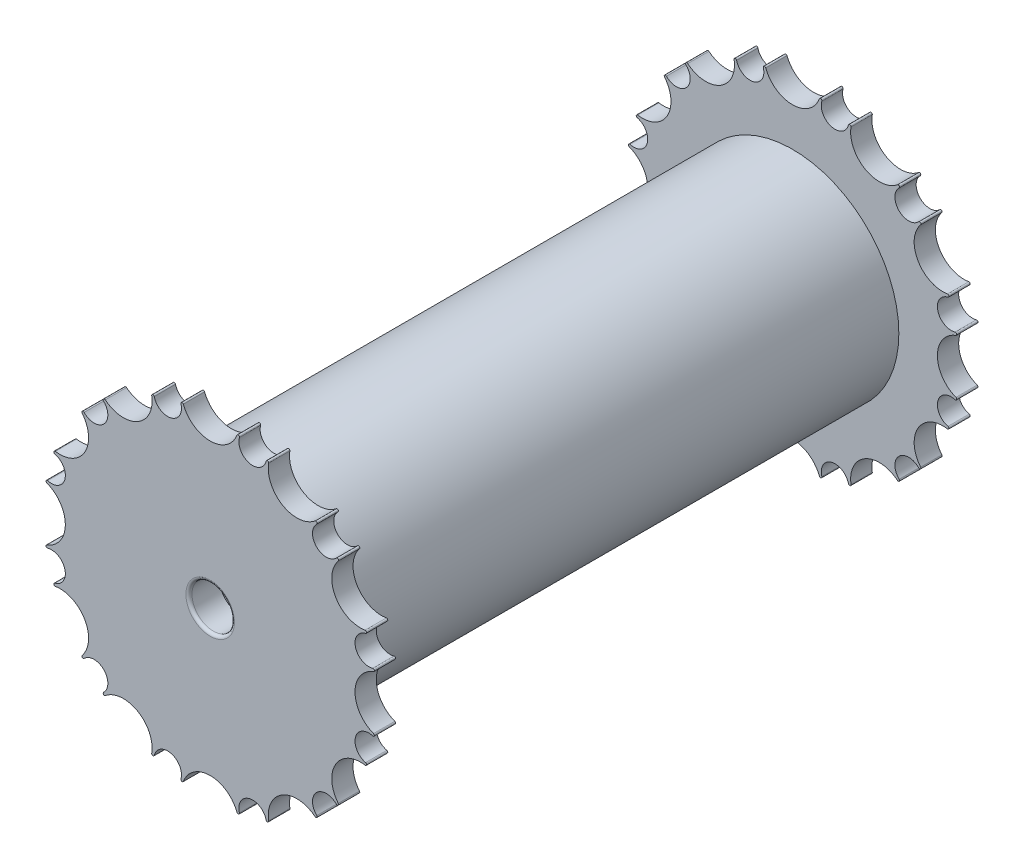
SolidWorks part; units mm, degrees
ref_plane "Front Plane" through (0, 0, 0) normal (0, 0, 1) x (1, 0, 0)
ref_plane "Top Plane" through (0, 0, 0) normal (0, 1, 0) x (1, 0, 0)
ref_plane "Right Plane" through (0, 0, 0) normal (1, 0, 0) x (0, 0, -1)
sketch "Sketch1" plane through (0, 0, 0) normal (0, 0, 1) x (1, 0, 0)
  line L1 (5, -18.6603) -> (13.6603, -13.6603)
  line L2 (13.6603, -13.6603) -> (18.6603, -5)
  line L3 (18.6603, -5) -> (18.6603, 5)
  line L4 (18.6603, 5) -> (13.6603, 13.6603)
  line L5 (13.6603, 13.6603) -> (5, 18.6603)
  line L6 (5, 18.6603) -> (-5, 18.6603)
  line L7 (-5, 18.6603) -> (-13.6603, 13.6603)
  line L8 (-13.6603, 13.6603) -> (-18.6603, 5)
  line L9 (-18.6603, 5) -> (-18.6603, -5)
  line L10 (-18.6603, -5) -> (-13.6603, -13.6603)
  line L11 (-13.6603, -13.6603) -> (-5, -18.6603)
  line L12 (-5, -18.6603) -> (5, -18.6603)
  circle A0 centre (0, 0) radius 18.6603 construction
  circle A1 centre (-5, 18.6603) radius 1.5 construction
  circle A2 centre (5, 18.6603) radius 1.5 construction
  circle A3 centre (-5, 18.6603) radius 1.625
  circle A4 centre (5, 18.6603) radius 1.625
  circle A5 centre (0, 20.4103) radius 3.375 construction
  arc A6 (-3.4408, 19.1179) -> (-3.1557, 19.2136) centre (-3.2964, 19.1603) cw
  arc A7 (3.1557, 19.2136) -> (3.4408, 19.1179) centre (3.2964, 19.1603) cw
  point P1 (0, 18.6603)
  dimension "D2" = 3
  dimension "D5" = 6.75
  dimension "D1" = 10
  dimension "D6" = 1.75
  dimension "D7" = 0.5
  dimension "D3" = 0.125
  dimension "D4" = 0.125
sketch "Sketch10" plane through (0, 0, 0) normal (0, 0, 1) x (1, 0, 0)
  line L2 (-5, -18.6603) -> (5, -18.6603) construction
  line L14 (-3.375, -18.6603) -> (-2.8858, -18.6603)
  circle A0 centre (5, 18.6603) radius 1.625 construction
  arc A1 (3.4408, 19.1179) -> (3.1557, 19.2136) centre (3.2964, 19.1603) ccw construction
  circle A2 centre (0, 20.4103) radius 3.375 construction
  arc A3 (-3.1557, 19.2136) -> (-3.4408, 19.1179) centre (-3.2964, 19.1603) ccw construction
  circle A4 centre (-5, 18.6603) radius 1.625 construction
  arc A5 (3.4408, 19.1179) -> (6.5791, 18.277) centre (5, 18.6603) ccw
  arc A6 (3.4408, 19.1179) -> (3.1557, 19.2136) centre (3.2964, 19.1603) ccw
  arc A7 (-3.1557, 19.2136) -> (3.1557, 19.2136) centre (0, 20.4103) ccw
  arc A8 (-3.1557, 19.2136) -> (-3.4408, 19.1179) centre (-3.2964, 19.1603) ccw
  arc A9 (-6.4073, 17.8478) -> (-3.4408, 19.1179) centre (-5, 18.6603) ccw
  circle A12 centre (0, 0) radius 12.5
  arc A14 (3.375, 18.6603) -> (6.5791, 18.277) centre (5, 18.6603) ccw
  arc A15 (6.8739, 18.2173) -> (6.5791, 18.277) centre (6.7254, 18.2415) ccw
  arc A16 (6.8739, 18.2173) -> (12.3397, 15.0616) centre (10.2051, 17.6758) ccw
  arc A17 (12.5387, 14.8362) -> (12.3397, 15.0616) centre (12.4349, 14.9451) ccw
  arc A18 (12.5387, 14.8362) -> (14.8362, 12.5387) centre (13.6603, 13.6603) ccw
  arc A19 (12.253, 14.4728) -> (14.8362, 12.5387) centre (13.6603, 13.6603) ccw
  arc A20 (15.0616, 12.3397) -> (14.8362, 12.5387) centre (14.9451, 12.4349) ccw
  arc A21 (15.0616, 12.3397) -> (18.2173, 6.8739) centre (17.6758, 10.2051) ccw
  arc A22 (18.277, 6.5791) -> (18.2173, 6.8739) centre (18.2415, 6.7254) ccw
  arc A23 (18.277, 6.5791) -> (19.1179, 3.4408) centre (18.6603, 5) ccw
  arc A24 (17.8478, 6.4073) -> (19.1179, 3.4408) centre (18.6603, 5) ccw
  arc A25 (19.2136, 3.1557) -> (19.1179, 3.4408) centre (19.1603, 3.2964) ccw
  arc A26 (19.2136, 3.1557) -> (19.2136, -3.1557) centre (20.4103, 0) ccw
  arc A27 (19.1179, -3.4408) -> (19.2136, -3.1557) centre (19.1603, -3.2964) ccw
  arc A28 (19.1179, -3.4408) -> (18.277, -6.5791) centre (18.6603, -5) ccw
  arc A29 (18.6603, -3.375) -> (18.277, -6.5791) centre (18.6603, -5) ccw
  arc A30 (18.2173, -6.8739) -> (18.277, -6.5791) centre (18.2415, -6.7254) ccw
  arc A31 (18.2173, -6.8739) -> (15.0616, -12.3397) centre (17.6758, -10.2051) ccw
  arc A32 (14.8362, -12.5387) -> (15.0616, -12.3397) centre (14.9451, -12.4349) ccw
  arc A33 (14.8362, -12.5387) -> (12.5387, -14.8362) centre (13.6603, -13.6603) ccw
  arc A34 (14.4728, -12.253) -> (12.5387, -14.8362) centre (13.6603, -13.6603) ccw
  arc A35 (12.3397, -15.0616) -> (12.5387, -14.8362) centre (12.4349, -14.9451) ccw
  arc A36 (12.3397, -15.0616) -> (6.8739, -18.2173) centre (10.2051, -17.6758) ccw
  arc A37 (6.5791, -18.277) -> (6.8739, -18.2173) centre (6.7254, -18.2415) ccw
  arc A38 (6.5791, -18.277) -> (3.4408, -19.1179) centre (5, -18.6603) ccw
  arc A39 (6.4073, -17.8478) -> (3.4408, -19.1179) centre (5, -18.6603) ccw
  arc A40 (3.1557, -19.2136) -> (3.4408, -19.1179) centre (3.2964, -19.1603) ccw
  arc A41 (3.1557, -19.2136) -> (-3.1557, -19.2136) centre (0, -20.4103) ccw
  arc A42 (-3.4408, -19.1179) -> (-3.1557, -19.2136) centre (-3.2964, -19.1603) ccw
  arc A43 (-3.4408, -19.1179) -> (-6.5791, -18.277) centre (-5, -18.6603) ccw
  arc A44 (-3.375, -18.6603) -> (-6.5791, -18.277) centre (-5, -18.6603) ccw
  arc A45 (-6.8739, -18.2173) -> (-6.5791, -18.277) centre (-6.7254, -18.2415) ccw
  arc A46 (-6.8739, -18.2173) -> (-12.3397, -15.0616) centre (-10.2051, -17.6758) ccw
  arc A47 (-12.5387, -14.8362) -> (-12.3397, -15.0616) centre (-12.4349, -14.9451) ccw
  arc A48 (-12.5387, -14.8362) -> (-14.8362, -12.5387) centre (-13.6603, -13.6603) ccw
  arc A49 (-12.253, -14.4728) -> (-14.8362, -12.5387) centre (-13.6603, -13.6603) ccw
  arc A50 (-15.0616, -12.3397) -> (-14.8362, -12.5387) centre (-14.9451, -12.4349) ccw
  arc A51 (-15.0616, -12.3397) -> (-18.2173, -6.8739) centre (-17.6758, -10.2051) ccw
  arc A52 (-18.277, -6.5791) -> (-18.2173, -6.8739) centre (-18.2415, -6.7254) ccw
  arc A53 (-18.277, -6.5791) -> (-19.1179, -3.4408) centre (-18.6603, -5) ccw
  arc A54 (-17.8478, -6.4073) -> (-19.1179, -3.4408) centre (-18.6603, -5) ccw
  arc A55 (-19.2136, -3.1557) -> (-19.1179, -3.4408) centre (-19.1603, -3.2964) ccw
  arc A56 (-19.2136, -3.1557) -> (-19.2136, 3.1557) centre (-20.4103, 0) ccw
  arc A57 (-19.1179, 3.4408) -> (-19.2136, 3.1557) centre (-19.1603, 3.2964) ccw
  arc A58 (-19.1179, 3.4408) -> (-18.277, 6.5791) centre (-18.6603, 5) ccw
  arc A59 (-18.6603, 3.375) -> (-18.277, 6.5791) centre (-18.6603, 5) ccw
  arc A60 (-18.2173, 6.8739) -> (-18.277, 6.5791) centre (-18.2415, 6.7254) ccw
  arc A61 (-18.2173, 6.8739) -> (-15.0616, 12.3397) centre (-17.6758, 10.2051) ccw
  arc A62 (-14.8362, 12.5387) -> (-15.0616, 12.3397) centre (-14.9451, 12.4349) ccw
  arc A63 (-14.8362, 12.5387) -> (-12.5387, 14.8362) centre (-13.6603, 13.6603) ccw
  arc A64 (-14.4728, 12.253) -> (-12.5387, 14.8362) centre (-13.6603, 13.6603) ccw
  arc A65 (-12.3397, 15.0616) -> (-12.5387, 14.8362) centre (-12.4349, 14.9451) ccw
  arc A66 (-12.3397, 15.0616) -> (-6.8739, 18.2173) centre (-10.2051, 17.6758) ccw
  arc A67 (-6.5791, 18.277) -> (-6.8739, 18.2173) centre (-6.7254, 18.2415) ccw
  arc A68 (-6.5791, 18.277) -> (-3.4408, 19.1179) centre (-5, 18.6603) ccw
  point P162 (0, 0)
  dimension "D2" = 25
  dimension "D1" = 12
sketch "Sketch2" plane through (0, 0, 0) normal (0, 0, 1) x (1, 0, 0)
  line L0 (-10, 37.3205) -> (0, 0) construction
  line L1 (0, 0) -> (10, 37.3205) construction
  arc A5 (6.8815, 38.2358) -> (6.3115, 38.4272) centre (6.5928, 38.3205) ccw
  arc A6 (6.8815, 38.2358) -> (9.1588, 34.1812) centre (10, 37.3205) ccw
  arc A7 (-6.3115, 38.4272) -> (6.3115, 38.4272) centre (0, 40.8205) ccw
  arc A8 (-6.3115, 38.4272) -> (-6.8815, 38.2358) centre (-6.5928, 38.3205) ccw
  arc A9 (-9.1588, 34.1812) -> (-6.8815, 38.2358) centre (-10, 37.3205) ccw
  arc A10 (9.1588, 34.1812) -> (13.1583, 36.5539) centre (10, 37.3205) ccw
  arc A11 (13.7477, 36.4347) -> (13.1583, 36.5539) centre (13.4507, 36.4829) ccw
  arc A12 (13.7477, 36.4347) -> (24.6795, 30.1232) centre (20.4103, 35.3516) ccw
  arc A13 (25.0775, 29.6724) -> (24.6795, 30.1232) centre (24.8698, 29.8901) ccw
  arc A14 (25.0775, 29.6724) -> (25.0224, 25.0224) centre (27.3205, 27.3205) ccw
  arc A15 (25.0224, 25.0224) -> (29.6724, 25.0775) centre (27.3205, 27.3205) ccw
  arc A16 (30.1232, 24.6795) -> (29.6724, 25.0775) centre (29.8901, 24.8698) ccw
  arc A17 (30.1232, 24.6795) -> (36.4347, 13.7477) centre (35.3516, 20.4103) ccw
  arc A18 (36.5539, 13.1583) -> (36.4347, 13.7477) centre (36.4829, 13.4507) ccw
  arc A19 (36.5539, 13.1583) -> (34.1812, 9.1588) centre (37.3205, 10) ccw
  arc A20 (34.1812, 9.1588) -> (38.2358, 6.8815) centre (37.3205, 10) ccw
  arc A21 (38.4272, 6.3115) -> (38.2358, 6.8815) centre (38.3205, 6.5928) ccw
  arc A22 (38.4272, 6.3115) -> (38.4272, -6.3115) centre (40.8205, 0) ccw
  arc A23 (38.2358, -6.8815) -> (38.4272, -6.3115) centre (38.3205, -6.5928) ccw
  arc A24 (38.2358, -6.8815) -> (34.1812, -9.1588) centre (37.3205, -10) ccw
  arc A25 (34.1812, -9.1588) -> (36.5539, -13.1583) centre (37.3205, -10) ccw
  arc A26 (36.4347, -13.7477) -> (36.5539, -13.1583) centre (36.4829, -13.4507) ccw
  arc A27 (36.4347, -13.7477) -> (30.1232, -24.6795) centre (35.3516, -20.4103) ccw
  arc A28 (29.6724, -25.0775) -> (30.1232, -24.6795) centre (29.8901, -24.8698) ccw
  arc A29 (29.6724, -25.0775) -> (25.0224, -25.0224) centre (27.3205, -27.3205) ccw
  arc A30 (25.0224, -25.0224) -> (25.0775, -29.6724) centre (27.3205, -27.3205) ccw
  arc A31 (24.6795, -30.1232) -> (25.0775, -29.6724) centre (24.8698, -29.8901) ccw
  arc A32 (24.6795, -30.1232) -> (13.7477, -36.4347) centre (20.4103, -35.3516) ccw
  arc A33 (13.1583, -36.5539) -> (13.7477, -36.4347) centre (13.4507, -36.4829) ccw
  arc A34 (13.1583, -36.5539) -> (9.1588, -34.1812) centre (10, -37.3205) ccw
  arc A35 (9.1588, -34.1812) -> (6.8815, -38.2358) centre (10, -37.3205) ccw
  arc A36 (6.3115, -38.4272) -> (6.8815, -38.2358) centre (6.5928, -38.3205) ccw
  arc A37 (6.3115, -38.4272) -> (-6.3115, -38.4272) centre (0, -40.8205) ccw
  arc A38 (-6.8815, -38.2358) -> (-6.3115, -38.4272) centre (-6.5928, -38.3205) ccw
  arc A39 (-6.8815, -38.2358) -> (-9.1588, -34.1812) centre (-10, -37.3205) ccw
  arc A40 (-9.1588, -34.1812) -> (-13.1583, -36.5539) centre (-10, -37.3205) ccw
  arc A41 (-13.7477, -36.4347) -> (-13.1583, -36.5539) centre (-13.4507, -36.4829) ccw
  arc A42 (-13.7477, -36.4347) -> (-24.6795, -30.1232) centre (-20.4103, -35.3516) ccw
  arc A43 (-25.0775, -29.6724) -> (-24.6795, -30.1232) centre (-24.8698, -29.8901) ccw
  arc A44 (-25.0775, -29.6724) -> (-25.0224, -25.0224) centre (-27.3205, -27.3205) ccw
  arc A45 (-25.0224, -25.0224) -> (-29.6724, -25.0775) centre (-27.3205, -27.3205) ccw
  arc A46 (-30.1232, -24.6795) -> (-29.6724, -25.0775) centre (-29.8901, -24.8698) ccw
  arc A47 (-30.1232, -24.6795) -> (-36.4347, -13.7477) centre (-35.3516, -20.4103) ccw
  arc A48 (-36.5539, -13.1583) -> (-36.4347, -13.7477) centre (-36.4829, -13.4507) ccw
  arc A49 (-36.5539, -13.1583) -> (-34.1812, -9.1588) centre (-37.3205, -10) ccw
  arc A50 (-34.1812, -9.1588) -> (-38.2358, -6.8815) centre (-37.3205, -10) ccw
  arc A51 (-38.4272, -6.3115) -> (-38.2358, -6.8815) centre (-38.3205, -6.5928) ccw
  arc A52 (-38.4272, -6.3115) -> (-38.4272, 6.3115) centre (-40.8205, 0) ccw
  arc A53 (-38.2358, 6.8815) -> (-38.4272, 6.3115) centre (-38.3205, 6.5928) ccw
  arc A54 (-38.2358, 6.8815) -> (-34.1812, 9.1588) centre (-37.3205, 10) ccw
  arc A55 (-34.1812, 9.1588) -> (-36.5539, 13.1583) centre (-37.3205, 10) ccw
  arc A56 (-36.4347, 13.7477) -> (-36.5539, 13.1583) centre (-36.4829, 13.4507) ccw
  arc A57 (-36.4347, 13.7477) -> (-30.1232, 24.6795) centre (-35.3516, 20.4103) ccw
  arc A58 (-29.6724, 25.0775) -> (-30.1232, 24.6795) centre (-29.8901, 24.8698) ccw
  arc A59 (-29.6724, 25.0775) -> (-25.0224, 25.0224) centre (-27.3205, 27.3205) ccw
  arc A60 (-25.0224, 25.0224) -> (-25.0775, 29.6724) centre (-27.3205, 27.3205) ccw
  arc A61 (-24.6795, 30.1232) -> (-25.0775, 29.6724) centre (-24.8698, 29.8901) ccw
  arc A62 (-24.6795, 30.1232) -> (-13.7477, 36.4347) centre (-20.4103, 35.3516) ccw
  arc A63 (-13.1583, 36.5539) -> (-13.7477, 36.4347) centre (-13.4507, 36.4829) ccw
  arc A64 (-13.1583, 36.5539) -> (-9.1588, 34.1812) centre (-10, 37.3205) ccw
  circle A65 centre (0, 0) radius 30
  point P139 (0, 0)
  dimension "D2" = 60
  dimension "D3" = 6.75
  dimension "D1" = 12
sketch "Sketch4" plane through (0, 0, 0) normal (0, 0, 1) x (1, 0, 0)
  arc A62 (-24.6795, 30.1232) -> (-25.0775, 29.6724) centre (-24.8698, 29.8901) ccw
  arc A63 (-24.6795, 30.1232) -> (-13.7477, 36.4347) centre (-20.4103, 35.3516) ccw
  arc A64 (-13.1583, 36.5539) -> (-13.7477, 36.4347) centre (-13.4507, 36.4829) ccw
  arc A65 (-13.1583, 36.5539) -> (-9.1588, 34.1812) centre (-10, 37.3205) ccw
  arc A66 (-9.1588, 34.1812) -> (-6.8815, 38.2358) centre (-10, 37.3205) ccw
  arc A67 (-6.3115, 38.4272) -> (-6.8815, 38.2358) centre (-6.5928, 38.3205) ccw
  arc A68 (-6.3115, 38.4272) -> (6.3115, 38.4272) centre (0, 40.8205) ccw
  arc A69 (6.8815, 38.2358) -> (6.3115, 38.4272) centre (6.5928, 38.3205) ccw
  arc A70 (6.8815, 38.2358) -> (9.1588, 34.1812) centre (10, 37.3205) ccw
  arc A71 (9.1588, 34.1812) -> (13.1583, 36.5539) centre (10, 37.3205) ccw
  arc A72 (13.7477, 36.4347) -> (13.1583, 36.5539) centre (13.4507, 36.4829) ccw
  arc A73 (13.7477, 36.4347) -> (24.6795, 30.1232) centre (20.4103, 35.3516) ccw
  arc A74 (25.0775, 29.6724) -> (24.6795, 30.1232) centre (24.8698, 29.8901) ccw
  arc A75 (25.0775, 29.6724) -> (25.0224, 25.0224) centre (27.3205, 27.3205) ccw
  arc A76 (25.0224, 25.0224) -> (29.6724, 25.0775) centre (27.3205, 27.3205) ccw
  arc A77 (30.1232, 24.6795) -> (29.6724, 25.0775) centre (29.8901, 24.8698) ccw
  arc A78 (30.1232, 24.6795) -> (36.4347, 13.7477) centre (35.3516, 20.4103) ccw
  arc A79 (36.5539, 13.1583) -> (36.4347, 13.7477) centre (36.4829, 13.4507) ccw
  arc A80 (36.5539, 13.1583) -> (34.1812, 9.1588) centre (37.3205, 10) ccw
  arc A81 (34.1812, 9.1588) -> (38.2358, 6.8815) centre (37.3205, 10) ccw
  arc A82 (38.4272, 6.3115) -> (38.2358, 6.8815) centre (38.3205, 6.5928) ccw
  arc A83 (38.4272, 6.3115) -> (38.4272, -6.3115) centre (40.8205, 0) ccw
  arc A84 (38.2358, -6.8815) -> (38.4272, -6.3115) centre (38.3205, -6.5928) ccw
  arc A85 (38.2358, -6.8815) -> (34.1812, -9.1588) centre (37.3205, -10) ccw
  arc A86 (34.1812, -9.1588) -> (36.5539, -13.1583) centre (37.3205, -10) ccw
  arc A87 (36.4347, -13.7477) -> (36.5539, -13.1583) centre (36.4829, -13.4507) ccw
  arc A88 (36.4347, -13.7477) -> (30.1232, -24.6795) centre (35.3516, -20.4103) ccw
  arc A89 (29.6724, -25.0775) -> (30.1232, -24.6795) centre (29.8901, -24.8698) ccw
  arc A90 (29.6724, -25.0775) -> (25.0224, -25.0224) centre (27.3205, -27.3205) ccw
  arc A91 (25.0224, -25.0224) -> (25.0775, -29.6724) centre (27.3205, -27.3205) ccw
  arc A92 (24.6795, -30.1232) -> (25.0775, -29.6724) centre (24.8698, -29.8901) ccw
  arc A93 (24.6795, -30.1232) -> (13.7477, -36.4347) centre (20.4103, -35.3516) ccw
  arc A94 (13.1583, -36.5539) -> (13.7477, -36.4347) centre (13.4507, -36.4829) ccw
  arc A95 (13.1583, -36.5539) -> (9.1588, -34.1812) centre (10, -37.3205) ccw
  arc A96 (9.1588, -34.1812) -> (6.8815, -38.2358) centre (10, -37.3205) ccw
  arc A97 (6.3115, -38.4272) -> (6.8815, -38.2358) centre (6.5928, -38.3205) ccw
  arc A98 (6.3115, -38.4272) -> (-6.3115, -38.4272) centre (0, -40.8205) ccw
  arc A99 (-6.8815, -38.2358) -> (-6.3115, -38.4272) centre (-6.5928, -38.3205) ccw
  arc A100 (-6.8815, -38.2358) -> (-9.1588, -34.1812) centre (-10, -37.3205) ccw
  arc A101 (-9.1588, -34.1812) -> (-13.1583, -36.5539) centre (-10, -37.3205) ccw
  arc A102 (-13.7477, -36.4347) -> (-13.1583, -36.5539) centre (-13.4507, -36.4829) ccw
  arc A103 (-13.7477, -36.4347) -> (-24.6795, -30.1232) centre (-20.4103, -35.3516) ccw
  arc A104 (-25.0775, -29.6724) -> (-24.6795, -30.1232) centre (-24.8698, -29.8901) ccw
  arc A105 (-25.0775, -29.6724) -> (-25.0224, -25.0224) centre (-27.3205, -27.3205) ccw
  arc A106 (-25.0224, -25.0224) -> (-29.6724, -25.0775) centre (-27.3205, -27.3205) ccw
  arc A107 (-30.1232, -24.6795) -> (-29.6724, -25.0775) centre (-29.8901, -24.8698) ccw
  arc A108 (-30.1232, -24.6795) -> (-36.4347, -13.7477) centre (-35.3516, -20.4103) ccw
  arc A109 (-36.5539, -13.1583) -> (-36.4347, -13.7477) centre (-36.4829, -13.4507) ccw
  arc A110 (-36.5539, -13.1583) -> (-34.1812, -9.1588) centre (-37.3205, -10) ccw
  arc A111 (-34.1812, -9.1588) -> (-38.2358, -6.8815) centre (-37.3205, -10) ccw
  arc A112 (-38.4272, -6.3115) -> (-38.2358, -6.8815) centre (-38.3205, -6.5928) ccw
  arc A113 (-38.4272, -6.3115) -> (-38.4272, 6.3115) centre (-40.8205, 0) ccw
  arc A114 (-38.2358, 6.8815) -> (-38.4272, 6.3115) centre (-38.3205, 6.5928) ccw
  arc A115 (-38.2358, 6.8815) -> (-34.1812, 9.1588) centre (-37.3205, 10) ccw
  arc A116 (-34.1812, 9.1588) -> (-36.5539, 13.1583) centre (-37.3205, 10) ccw
  arc A117 (-36.4347, 13.7477) -> (-36.5539, 13.1583) centre (-36.4829, 13.4507) ccw
  arc A118 (-36.4347, 13.7477) -> (-30.1232, 24.6795) centre (-35.3516, 20.4103) ccw
  arc A119 (-29.6724, 25.0775) -> (-30.1232, 24.6795) centre (-29.8901, 24.8698) ccw
  arc A120 (-29.6724, 25.0775) -> (-25.0224, 25.0224) centre (-27.3205, 27.3205) ccw
  arc A121 (-25.0224, 25.0224) -> (-25.0775, 29.6724) centre (-27.3205, 27.3205) ccw
  arc A122 (-24.6795, 30.1232) -> (-25.0775, 29.6724) centre (-24.8698, 29.8901) ccw
  arc A123 (-24.6795, 30.1232) -> (-13.7477, 36.4347) centre (-20.4103, 35.3516) ccw
  arc A124 (-13.1583, 36.5539) -> (-13.7477, 36.4347) centre (-13.4507, 36.4829) ccw
  arc A125 (-13.1583, 36.5539) -> (-9.1588, 34.1812) centre (-10, 37.3205) ccw
  arc A126 (-9.1588, 34.1812) -> (-6.8815, 38.2358) centre (-10, 37.3205) ccw
  arc A127 (-6.3115, 38.4272) -> (-6.8815, 38.2358) centre (-6.5928, 38.3205) ccw
  arc A128 (-6.3115, 38.4272) -> (6.3115, 38.4272) centre (0, 40.8205) ccw
  arc A129 (6.8815, 38.2358) -> (6.3115, 38.4272) centre (6.5928, 38.3205) ccw
  arc A130 (6.8815, 38.2358) -> (9.1588, 34.1812) centre (10, 37.3205) ccw
  arc A131 (9.1588, 34.1812) -> (13.1583, 36.5539) centre (10, 37.3205) ccw
  arc A132 (13.7477, 36.4347) -> (13.1583, 36.5539) centre (13.4507, 36.4829) ccw
  arc A133 (13.7477, 36.4347) -> (24.6795, 30.1232) centre (20.4103, 35.3516) ccw
  arc A134 (25.0775, 29.6724) -> (24.6795, 30.1232) centre (24.8698, 29.8901) ccw
  arc A135 (25.0775, 29.6724) -> (25.0224, 25.0224) centre (27.3205, 27.3205) ccw
  arc A136 (25.0224, 25.0224) -> (29.6724, 25.0775) centre (27.3205, 27.3205) ccw
  arc A137 (30.1232, 24.6795) -> (29.6724, 25.0775) centre (29.8901, 24.8698) ccw
  arc A138 (30.1232, 24.6795) -> (36.4347, 13.7477) centre (35.3516, 20.4103) ccw
  arc A139 (36.5539, 13.1583) -> (36.4347, 13.7477) centre (36.4829, 13.4507) ccw
  arc A140 (36.5539, 13.1583) -> (34.1812, 9.1588) centre (37.3205, 10) ccw
  arc A141 (34.1812, 9.1588) -> (38.2358, 6.8815) centre (37.3205, 10) ccw
  arc A142 (38.4272, 6.3115) -> (38.2358, 6.8815) centre (38.3205, 6.5928) ccw
  arc A143 (38.4272, 6.3115) -> (38.4272, -6.3115) centre (40.8205, 0) ccw
  arc A144 (38.2358, -6.8815) -> (38.4272, -6.3115) centre (38.3205, -6.5928) ccw
  arc A145 (38.2358, -6.8815) -> (34.1812, -9.1588) centre (37.3205, -10) ccw
  arc A146 (34.1812, -9.1588) -> (36.5539, -13.1583) centre (37.3205, -10) ccw
  arc A147 (36.4347, -13.7477) -> (36.5539, -13.1583) centre (36.4829, -13.4507) ccw
  arc A148 (36.4347, -13.7477) -> (30.1232, -24.6795) centre (35.3516, -20.4103) ccw
  arc A149 (29.6724, -25.0775) -> (30.1232, -24.6795) centre (29.8901, -24.8698) ccw
  arc A150 (29.6724, -25.0775) -> (25.0224, -25.0224) centre (27.3205, -27.3205) ccw
  arc A151 (25.0224, -25.0224) -> (25.0775, -29.6724) centre (27.3205, -27.3205) ccw
  arc A152 (24.6795, -30.1232) -> (25.0775, -29.6724) centre (24.8698, -29.8901) ccw
  arc A153 (24.6795, -30.1232) -> (13.7477, -36.4347) centre (20.4103, -35.3516) ccw
  arc A154 (13.1583, -36.5539) -> (13.7477, -36.4347) centre (13.4507, -36.4829) ccw
  arc A155 (13.1583, -36.5539) -> (9.1588, -34.1812) centre (10, -37.3205) ccw
  arc A156 (9.1588, -34.1812) -> (6.8815, -38.2358) centre (10, -37.3205) ccw
  arc A157 (6.3115, -38.4272) -> (6.8815, -38.2358) centre (6.5928, -38.3205) ccw
  arc A158 (6.3115, -38.4272) -> (-6.3115, -38.4272) centre (0, -40.8205) ccw
  arc A159 (-6.8815, -38.2358) -> (-6.3115, -38.4272) centre (-6.5928, -38.3205) ccw
  arc A160 (-6.8815, -38.2358) -> (-9.1588, -34.1812) centre (-10, -37.3205) ccw
  arc A161 (-9.1588, -34.1812) -> (-13.1583, -36.5539) centre (-10, -37.3205) ccw
  arc A162 (-13.7477, -36.4347) -> (-13.1583, -36.5539) centre (-13.4507, -36.4829) ccw
  arc A163 (-13.7477, -36.4347) -> (-24.6795, -30.1232) centre (-20.4103, -35.3516) ccw
  arc A164 (-25.0775, -29.6724) -> (-24.6795, -30.1232) centre (-24.8698, -29.8901) ccw
  arc A165 (-25.0775, -29.6724) -> (-25.0224, -25.0224) centre (-27.3205, -27.3205) ccw
  arc A166 (-25.0224, -25.0224) -> (-29.6724, -25.0775) centre (-27.3205, -27.3205) ccw
  arc A167 (-30.1232, -24.6795) -> (-29.6724, -25.0775) centre (-29.8901, -24.8698) ccw
  arc A168 (-30.1232, -24.6795) -> (-36.4347, -13.7477) centre (-35.3516, -20.4103) ccw
  arc A169 (-36.5539, -13.1583) -> (-36.4347, -13.7477) centre (-36.4829, -13.4507) ccw
  arc A170 (-36.5539, -13.1583) -> (-34.1812, -9.1588) centre (-37.3205, -10) ccw
  arc A171 (-34.1812, -9.1588) -> (-38.2358, -6.8815) centre (-37.3205, -10) ccw
  arc A172 (-38.4272, -6.3115) -> (-38.2358, -6.8815) centre (-38.3205, -6.5928) ccw
  arc A173 (-38.4272, -6.3115) -> (-38.4272, 6.3115) centre (-40.8205, 0) ccw
  arc A174 (-38.2358, 6.8815) -> (-38.4272, 6.3115) centre (-38.3205, 6.5928) ccw
  arc A175 (-38.2358, 6.8815) -> (-34.1812, 9.1588) centre (-37.3205, 10) ccw
  arc A176 (-34.1812, 9.1588) -> (-36.5539, 13.1583) centre (-37.3205, 10) ccw
  arc A177 (-36.4347, 13.7477) -> (-36.5539, 13.1583) centre (-36.4829, 13.4507) ccw
  arc A178 (-36.4347, 13.7477) -> (-30.1232, 24.6795) centre (-35.3516, 20.4103) ccw
  arc A179 (-29.6724, 25.0775) -> (-30.1232, 24.6795) centre (-29.8901, 24.8698) ccw
  arc A180 (-29.6724, 25.0775) -> (-25.0224, 25.0224) centre (-27.3205, 27.3205) ccw
  arc A181 (-25.0224, 25.0224) -> (-25.0775, 29.6724) centre (-27.3205, 27.3205) ccw
  dimension "D2" = 0
extrude "Boss-Extrude1" add sketch "Sketch4" along normal mid plane 5
sketch "Sketch5" plane through (0, 0, 0) normal (0, 0, 1) x (1, 0, 0)
  circle A0 centre (0, 0) radius 10
  circle A1 centre (0, 0) radius 20
  dimension "D1" = 20
  dimension "D2" = 10
extrude "Boss-Extrude2" add sketch "Sketch5" along normal mid plane 2 separate body
sketch "Sketch6" plane through (0, 0, 1) normal (0, 0, 1) x (1, 0, 0)
  line L0 (0, 29.9906) -> (0, 19.9906) construction
  line L1 (0.75, 29.9906) -> (0.75, 19.9906)
  line L2 (-0.75, 29.9906) -> (-0.75, 19.9906)
  line L3 (25.5976, 15.6448) -> (16.9374, 10.6448)
  line L4 (26.3476, 14.3458) -> (17.6874, 9.3458)
  line L5 (25.9726, 14.9953) -> (17.3124, 9.9953) construction
  line L6 (26.3476, -14.3458) -> (17.6874, -9.3458)
  line L7 (25.5976, -15.6448) -> (16.9374, -10.6448)
  line L8 (25.9726, -14.9953) -> (17.3124, -9.9953) construction
  line L9 (0.75, -29.9906) -> (0.75, -19.9906)
  line L10 (-0.75, -29.9906) -> (-0.75, -19.9906)
  line L11 (0, -29.9906) -> (0, -19.9906) construction
  line L12 (-25.5976, -15.6448) -> (-16.9374, -10.6448)
  line L13 (-26.3476, -14.3458) -> (-17.6874, -9.3458)
  line L14 (-25.9726, -14.9953) -> (-17.3124, -9.9953) construction
  line L15 (-26.3476, 14.3458) -> (-17.6874, 9.3458)
  line L16 (-25.5976, 15.6448) -> (-16.9374, 10.6448)
  line L17 (-25.9726, 14.9953) -> (-17.3124, 9.9953) construction
  arc A0 (0.75, 29.9906) -> (-0.75, 29.9906) centre (0, 29.9906) ccw
  arc A1 (-0.75, 19.9906) -> (0.75, 19.9906) centre (0, 19.9906) ccw
  circle A2 centre (0, 0) radius 30 construction
  arc A3 (26.3476, 14.3458) -> (25.5976, 15.6448) centre (25.9726, 14.9953) ccw
  arc A4 (16.9374, 10.6448) -> (17.6874, 9.3458) centre (17.3124, 9.9953) ccw
  arc A5 (25.5976, -15.6448) -> (26.3476, -14.3458) centre (25.9726, -14.9953) ccw
  arc A6 (17.6874, -9.3458) -> (16.9374, -10.6448) centre (17.3124, -9.9953) ccw
  arc A7 (-0.75, -29.9906) -> (0.75, -29.9906) centre (0, -29.9906) ccw
  arc A8 (0.75, -19.9906) -> (-0.75, -19.9906) centre (0, -19.9906) ccw
  arc A9 (-26.3476, -14.3458) -> (-25.5976, -15.6448) centre (-25.9726, -14.9953) ccw
  arc A10 (-16.9374, -10.6448) -> (-17.6874, -9.3458) centre (-17.3124, -9.9953) ccw
  arc A11 (-25.5976, 15.6448) -> (-26.3476, 14.3458) centre (-25.9726, 14.9953) ccw
  arc A12 (-17.6874, 9.3458) -> (-16.9374, 10.6448) centre (-17.3124, 9.9953) ccw
  point P3 (0, 24.9906)
  point P14 (21.6425, 12.4953)
  point P21 (21.6425, -12.4953)
  point P28 (0, -24.9906)
  point P35 (-21.6425, -12.4953)
  point P42 (-21.6425, 12.4953)
  point P47 (0, 0)
  dimension "D1" = 1.5
  dimension "D2" = 10
  dimension "D3" = 6
extrude "Boss-Extrude3" add sketch "Sketch6" against normal blind 1.5
ref_plane "Plane1" through (0, 0, 68.5) normal (0, 0, 1) x (1, 0, 0)
mirror "Mirror2" about plane through (0, 0, 68.5) normal (0, 0, 1) of bodies 103
sketch "Sketch9" plane through (0, 0, 68.5) normal (0, 0, 1) x (1, 0, 0)
  circle A0 centre (0, 0) radius 25
  dimension "D1" = 50
extrude "Boss-Extrude4" add sketch "Sketch9" against normal up to surface and the other way up to surface
scale "Scale1" scale about origin uniform scaling yes scale factor 0.7
sketch "Sketch11" plane through (0, 0, 97.65) normal (0, 0, 1) x (1, 0, 0)
  circle A0 centre (0, 0) radius 3.5
  dimension "D1" = 7
sketch "Sketch12" plane through (0, 0, -1.75) normal (0, 0, -1) x (-1, 0, 0)
  circle A0 centre (0, 0) radius 3.5
  dimension "D1" = 7
extrude "Cut-Extrude1" cut sketch "Sketch11" against normal blind 5 contours A0
extrude "Cut-Extrude2" cut sketch "Sketch12" against normal blind 5 contours A0
fillet "Fillet1" radius 0.5 2 edges at (3.5, 0, 97.65) (-3.5, 0, -1.75)
